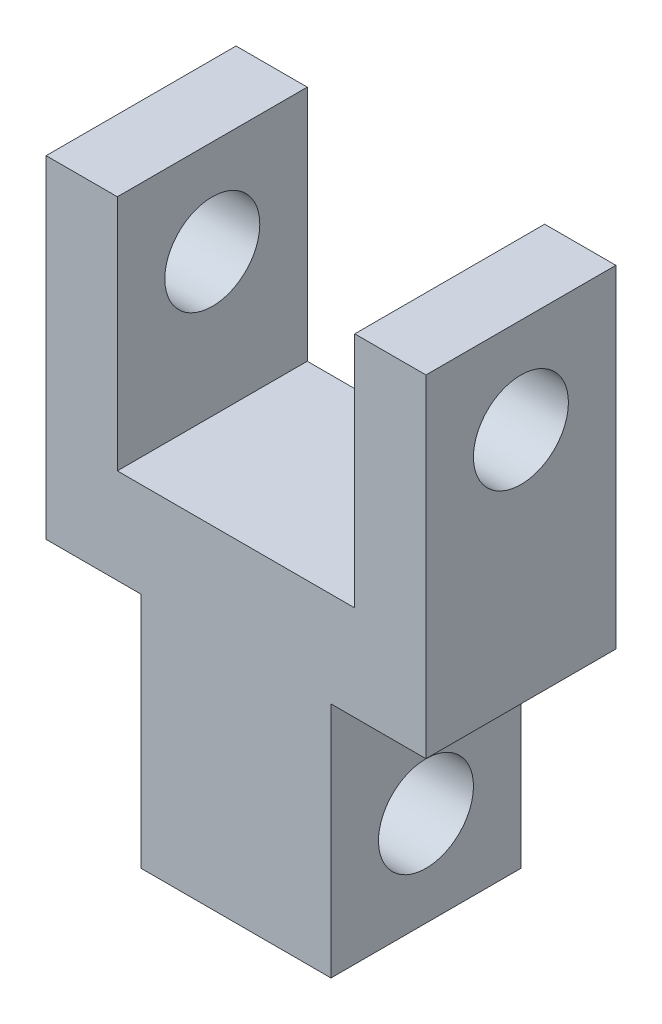
SolidWorks part; units mm, degrees
ref_plane "Front Plane" through (0, 0, 0) normal (0, 0, 1) x (1, 0, 0)
ref_plane "Top Plane" through (0, 0, 0) normal (0, 1, 0) x (1, 0, 0)
ref_plane "Right Plane" through (0, 0, 0) normal (1, 0, 0) x (0, 0, -1)
sketch "Sketch1" plane through (0, 0, 0) normal (0, 0, 1) x (1, 0, 0)
  line L0 (0, 35.3907) -> (0, -42.0511) construction
  line L1 (-12.7, 38.1) -> (-12.7, 15.875)
  line L2 (-12.7, 15.875) -> (-6.35, 15.875)
  line L3 (-6.35, 15.875) -> (-6.35, 0)
  line L4 (-6.35, 0) -> (6.35, 0)
  line L5 (-12.7, 38.1) -> (-7.9375, 38.1)
  line L6 (-7.9375, 38.1) -> (-7.9375, 22.225)
  line L7 (-7.9375, 22.225) -> (7.9375, 22.225)
  line L8 (6.35, 15.875) -> (6.35, 0)
  line L9 (12.7, 15.875) -> (6.35, 15.875)
  line L10 (12.7, 38.1) -> (12.7, 15.875)
  line L11 (12.7, 38.1) -> (7.9375, 38.1)
  line L12 (7.9375, 38.1) -> (7.9375, 22.225)
  point P12 (0, 0)
  point P17 (0, 10.6426)
  dimension "D1" = 4.7625
  dimension "D2" = 15.875
  dimension "D3" = 6.35
  dimension "D4" = 25.4
  dimension "D5" = 38.1
  dimension "D6" = 6.35
extrude "Boss-Extrude1" add sketch "Sketch1" along normal mid plane 12.7
sketch "Sketch2" plane through (12.7, 0, 0) normal (1, 0, 0) x (0, 0, -1)
  line L0 (0, 17.6048) -> (0, -49.379) construction
  line L1 (-6.35, 38.1) -> (6.35, 38.1) construction
  circle A0 centre (0, 31.75) radius 3.175
  dimension "D1" = 6.35
  dimension "D2" = 6.35
extrude "Cut-Extrude1" cut sketch "Sketch2" against normal through all
sketch "Sketch3" plane through (6.35, 0, 0) normal (1, 0, 0) x (0, 0, -1)
  line L0 (0, -21.828) -> (0, -46.0798) construction
  line L1 (-6.35, 0) -> (6.35, 0) construction
  circle A0 centre (0, 6.35) radius 3.175
  dimension "D1" = 6.35
  dimension "D2" = 6.35
extrude "Cut-Extrude2" cut sketch "Sketch3" against normal through all
